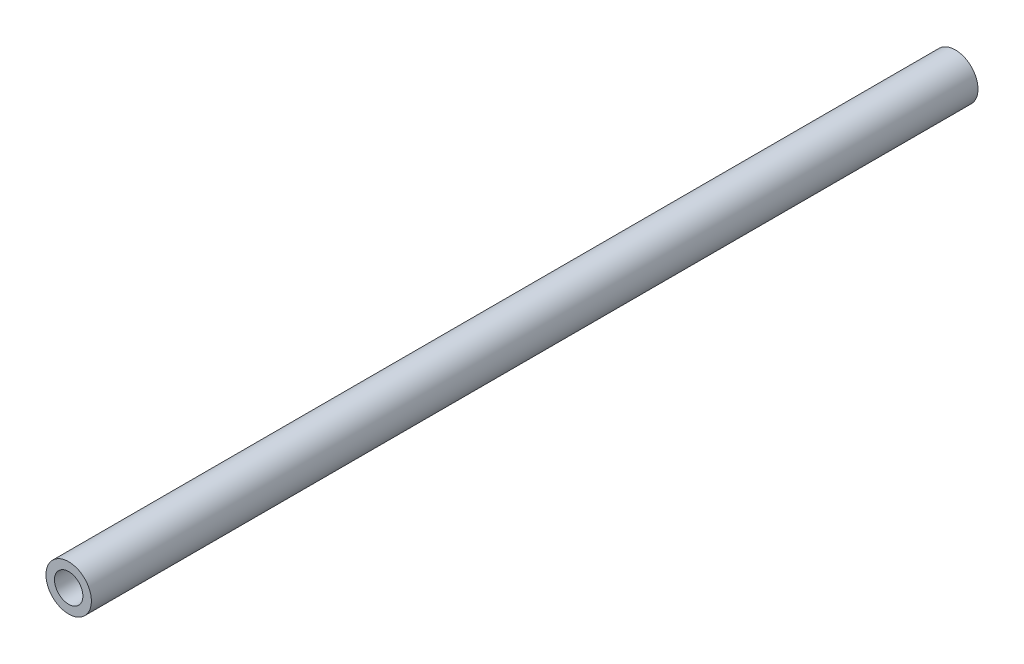
SolidWorks part; units mm, degrees
ref_plane "Front Plane" through (0, 0, 0) normal (0, 0, 1) x (1, 0, 0)
ref_plane "Top Plane" through (0, 0, 0) normal (0, 1, 0) x (1, 0, 0)
ref_plane "Right Plane" through (0, 0, 0) normal (1, 0, 0) x (0, 0, -1)
sketch "Sketch1" plane through (0, 0, 0) normal (0, 0, 1) x (1, 0, 0)
  circle A0 centre (0, 0) radius 1.5875
extrude "Boss-Extrude1" add sketch "Sketch1" along normal blind 61.976
sketch "Sketch2" plane through (0, 0, 61.976) normal (0, 0, 1) x (1, 0, 0)
  circle A0 centre (0, 0) radius 0.9922
extrude "Cut-Extrude1" cut sketch "Sketch2" against normal up to next
